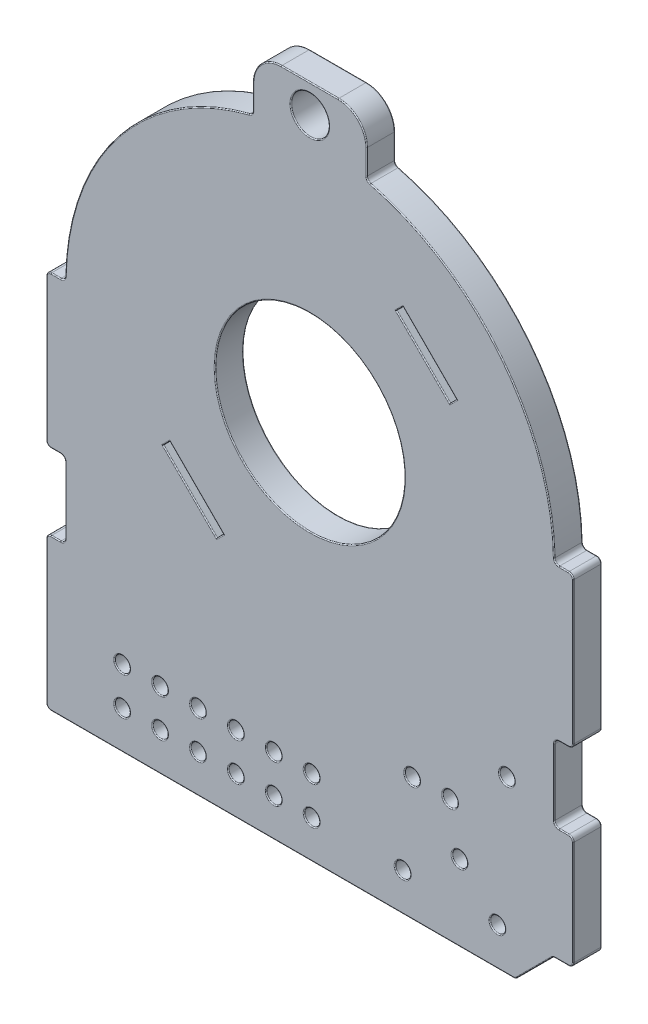
SolidWorks part; units mm, degrees
ref_plane "Ön Düzlem" through (0, 0, 0) normal (0, 0, 1) x (1, 0, 0)
ref_plane "Üst Düzlem" through (0, 0, 0) normal (0, 1, 0) x (1, 0, 0)
ref_plane "Sağ Düzlem" through (0, 0, 0) normal (1, 0, 0) x (0, 0, -1)
sketch "Sketch1" plane through (0, 0, 0) normal (0, 0, 1) x (1, 0, 0)
  line L0 (13.1476, 0) -> (13.65, 0)
  line L1 (-13.65, 0) -> (-13.1476, 0)
  line L2 (-13.9, -0.25) -> (-13.9, -7.75)
  line L3 (-13.65, -20) -> (10.7418, -20)
  line L4 (13.9, -0.25) -> (13.9, -7.75)
  line L5 (0, 15.5463) -> (0, 12.9) construction
  line L6 (-3, 12.7421) -> (-3, 14.0463)
  line L7 (0, -20) -> (0, 12.9) construction
  line L8 (12.7722, -18.0732) -> (10.9186, -19.9268)
  line L9 (13.65, -18) -> (12.949, -18)
  line L10 (13.9, -12.25) -> (13.9, -17.75)
  line L11 (13.65, -8) -> (13.15, -8)
  line L12 (-13.65, -12) -> (-13.15, -12)
  line L13 (13.65, -12) -> (13.15, -12)
  line L14 (12.9, -8.25) -> (12.9, -11.75)
  line L15 (-12.9, -8.25) -> (-12.9, -11.75)
  line L16 (-13.65, -8) -> (-13.15, -8)
  line L17 (-13.9, -12.25) -> (-13.9, -19.75)
  line L18 (-1.5, 15.5463) -> (1.5, 15.5463)
  line L19 (3, 14.0463) -> (3, 12.7421)
  line L20 (3, 14.0463) -> (-3, 14.0463) construction
  arc A0 (12.8977, 0.2452) -> (3.1882, 12.4998) centre (0, 0) ccw
  arc A1 (-12.8977, 0.2452) -> (-13.1476, 0) centre (-13.1476, 0.25) cw
  arc A2 (-13.65, 0) -> (-13.9, -0.25) centre (-13.65, -0.25) ccw
  arc A3 (12.8977, 0.2452) -> (13.1476, 0) centre (13.1476, 0.25) ccw
  arc A4 (13.65, 0) -> (13.9, -0.25) centre (13.65, -0.25) cw
  arc A5 (13.65, -18) -> (13.9, -17.75) centre (13.65, -17.75) ccw
  arc A6 (12.7722, -18.0732) -> (12.949, -18) centre (12.949, -18.25) cw
  arc A7 (10.9186, -19.9268) -> (10.7418, -20) centre (10.7418, -19.75) cw
  arc A8 (-13.65, -20) -> (-13.9, -19.75) centre (-13.65, -19.75) cw
  arc A9 (-3.1882, 12.4998) -> (-12.8977, 0.2452) centre (0, 0) ccw
  arc A10 (-3.1882, 12.4998) -> (-3, 12.7421) centre (-3.25, 12.7421) ccw
  circle A11 centre (0, 0) radius 12.9 construction
  arc A12 (-13.65, -8) -> (-13.9, -7.75) centre (-13.65, -7.75) cw
  arc A13 (-13.65, -12) -> (-13.9, -12.25) centre (-13.65, -12.25) ccw
  arc A14 (-13.15, -12) -> (-12.9, -11.75) centre (-13.15, -11.75) ccw
  arc A15 (-12.9, -8.25) -> (-13.15, -8) centre (-13.15, -8.25) ccw
  arc A16 (13.15, -8) -> (12.9, -8.25) centre (13.15, -8.25) ccw
  arc A17 (13.65, -8) -> (13.9, -7.75) centre (13.65, -7.75) ccw
  arc A18 (13.15, -12) -> (12.9, -11.75) centre (13.15, -11.75) cw
  arc A19 (13.9, -12.25) -> (13.65, -12) centre (13.65, -12.25) ccw
  circle A20 centre (10.4, -11) radius 0.4
  circle A21 centre (7.9, -16) radius 0.4
  circle A22 centre (9.9, -18) radius 0.4
  circle A23 centre (4.9, -18) radius 0.4
  circle A24 centre (7.4, -13.5) radius 0.4
  circle A25 centre (5.4, -13.5) radius 0.4
  arc A26 (3.1882, 12.4998) -> (3, 12.7421) centre (3.25, 12.7421) cw
  arc A27 (-3, 14.0463) -> (-1.5, 15.5463) centre (-1.5, 14.0463) cw
  arc A28 (1.5, 15.5463) -> (3, 14.0463) centre (1.5, 14.0463) cw
  circle A29 centre (0, 14.0463) radius 1
  circle A30 centre (0.1, -18) radius 0.4
  circle A31 centre (-1.9, -18) radius 0.4
  circle A32 centre (-3.9, -18) radius 0.4
  circle A33 centre (-5.9, -18) radius 0.4
  circle A34 centre (-7.9, -18) radius 0.4
  circle A35 centre (-9.9, -18) radius 0.4
  circle A36 centre (-1.9, -16) radius 0.4
  circle A37 centre (-3.9, -16) radius 0.4
  circle A38 centre (-5.9, -16) radius 0.4
  circle A39 centre (-7.9, -16) radius 0.4
  circle A40 centre (-9.9, -16) radius 0.4
  circle A41 centre (0.1, -16) radius 0.4
  point P18 (-13.9, 0)
  point P21 (12.9, 0)
  point P26 (13.9, -18)
  point P29 (12.8454, -18)
  point P32 (10.8454, -20)
  point P39 (-3, 12.5463)
  point P53 (-13.9, -8)
  point P56 (-13.9, -12)
  point P59 (-12.9, -12)
  point P62 (-12.9, -8)
  point P65 (12.9, -8)
  point P68 (13.9, -8)
  point P71 (12.9, -12)
  point P74 (13.9, -12)
  point P87 (3, 12.5463)
  point P92 (3, 15.5463)
  dimension "D1" = 25.8
  dimension "D4" = 0.25
  dimension "D11" = 0.25
  dimension "D12" = 0.8
  dimension "D13" = 2.5
  dimension "D14" = 9
  dimension "D15" = 0.8
  dimension "D16" = 0.8
  dimension "D17" = 0.8
  dimension "D18" = 2
  dimension "D19" = 2
  dimension "D20" = 5
  dimension "D21" = 4
  dimension "D22" = 4
  dimension "D23" = 2
  dimension "D24" = 0.8
  dimension "D25" = 0.8
  dimension "D26" = 2
  dimension "D27" = 6.5
  dimension "D28" = 0
  dimension "D5" = 0.25
  dimension "D29" = 0.25
  dimension "D30" = 1.5
  dimension "D32" = 2
  dimension "D33" = 0.8
  dimension "D36" = 2
  dimension "D37" = 4
  dimension "D38" = 6.5
  dimension "D2" = 13.9
  dimension "D3" = 13.9
  dimension "D6" = 3
  dimension "D7" = 3
  dimension "D8" = 8
  dimension "D9" = 4
  dimension "D10" = 1
  dimension "D31" = 1.5
  dimension "D35" = 6
  dimension "D34" = 2
extrude "Boss-Extrude1" add sketch "Sketch1" along normal blind 1.5
sketch "Sketch2" plane through (0, 0, 1.5) normal (0, 0, 1) x (1, 0, 0)
  line L0 (-12.9, 0) -> (12.9, 0) construction
  line L2 (4.5608, 7.3893) -> (4.9144, 7.7428)
  line L3 (7.3893, 4.5608) -> (4.5608, 7.3893)
  line L4 (7.7428, 4.9144) -> (7.3893, 4.5608)
  line L5 (-9.1217, -9.1217) -> (9.0267, 9.0267) construction
  line L6 (4.9144, 7.7428) -> (7.7428, 4.9144)
  line L10 (-7.7428, -4.9144) -> (-4.9144, -7.7428)
  line L11 (-4.9144, -7.7428) -> (-4.5608, -7.3893)
  line L12 (-4.5608, -7.3893) -> (-7.3893, -4.5608)
  line L13 (-7.3893, -4.5608) -> (-7.7428, -4.9144)
  circle A0 centre (0, 0) radius 5
  circle A1 centre (0, 0) radius 12.9 construction
  dimension "D1" = 10
  dimension "D2" = 16.9
  dimension "D3" = 8.45
  dimension "D6" = 4
  dimension "D7" = 0.5
  dimension "D8" = 2
  dimension "D10" = 45
  dimension "D11" = 0
extrude "Cut-Extrude1" cut sketch "Sketch2" against normal through all
fillet "Fillet1" radius 0.05 54 edges at (5, 0, 1.5) (10.111, 8.0111, 0) (5, 0, 0) (7.566, 4.7376, 1.5) (6.3286, 6.3286, 1.5) (-4.7376, -7.566, 1.5) (-7.566, -4.7376, 1.5) (-13.3988, 0, 0) (-13.9, -4, 0) (13.3988, 0, 1.5) (13.9, -4, 1.5) (-1.4541, -20, 1.5) (13.2995, -18, 0) (13.2995, -18, 1.5) (12.8533, -18.019, 0) (13.8268, -17.9268, 0) (-12.9725, 0.0716, 0) (13.8268, -17.9268, 1.5) (-13.8268, -0.0732, 1.5) (-12.9, -10, 0) (-13.4, -12, 0) (-13.9, -16, 0) (13.4, -8, 1.5) (12.9, -10, 1.5) (13.9, -15, 1.5) (-13.9, -16, 1.5) (-13.4, -12, 1.5) (-12.9, -10, 1.5) (-13.8268, -7.9268, 0) (-12.9732, -8.0732, 0) (-12.9732, -11.9268, 0) (13.8268, -12.0732, 0) (12.9732, -8.0732, 0) (13.8268, -7.9268, 1.5) (12.9732, -8.0732, 1.5) (-12.9732, -8.0732, 1.5) (5.8, -13.5, 1.5) (-13.8268, -19.9268, 1.5) (3, 13.3942, 0) (2.5607, 15.107, 0) (0, 15.5463, 0) (-2.5607, 15.107, 0) (-3, 13.3942, 0) (-10.111, 8.0111, 0) (1, 14.0463, 1.5) (-10.111, 8.0111, 1.5) (-3.0526, 12.5887, 1.5) (0, 15.5463, 1.5) (0.5, -16, 1.5) (-9.5, -18, 1.5) (-5.5, -18, 1.5) (0.5, -18, 1.5) (-5.5, -16, 1.5) (-9.5, -16, 1.5)
